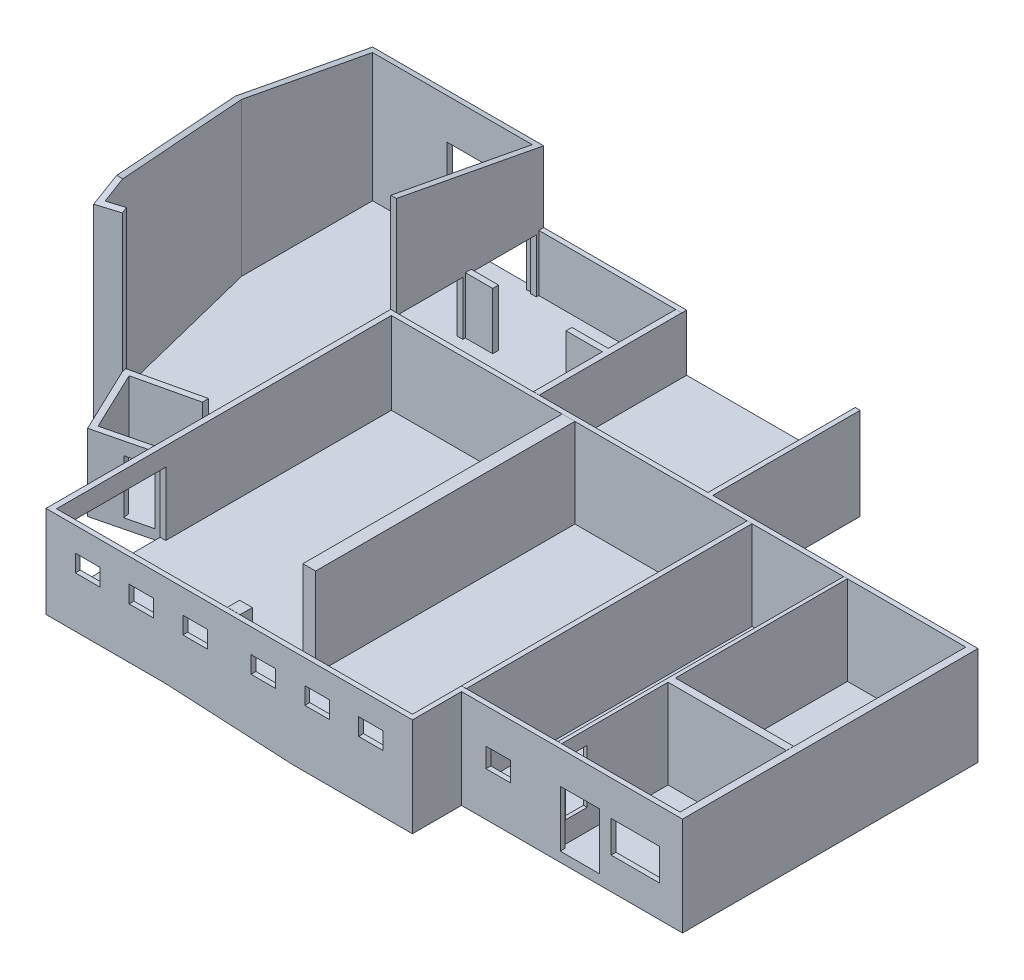
SolidWorks part; units mm, degrees
ref_plane "Ebene vorne" through (0, 0, 0) normal (0, 0, 1) x (1, 0, 0)
ref_plane "Ebene oben" through (0, 0, 0) normal (0, 1, 0) x (1, 0, 0)
ref_plane "Ebene rechts" through (0, 0, 0) normal (1, 0, 0) x (0, 0, -1)
sketch "Skizze1" plane through (0, 0, 0) normal (0, 1, 0) x (1, 0, 0)
  line L0 (14990, -18120) -> (14990, -20130)
  line L1 (0, 0) -> (13180, 0)
  line L4 (24030, -6030) -> (24030, -18120)
  line L5 (13180, 0) -> (13180, -6030)
  line L6 (13180, -6030) -> (24030, -6030)
  line L7 (14990, -20130) -> (0, -20130)
  line L8 (0, -20130) -> (0, 0)
  line L9 (14990, -18120) -> (24030, -18120)
  point P0 (0, 0)
  dimension "D1" = 14990
  dimension "D2" = 20130
  dimension "D3" = 9040
  dimension "D4" = 2010
  dimension "D5" = 13180
  dimension "D6" = 6030
extrude "Aufsatz-Linear austragen4" add sketch "Skizze1" along normal blind 250
sketch "Skizze5" plane through (0, 250, 0) normal (0, 1, 0) x (1, 0, 0)
  line L0 (23730, -6230) -> (23730, -17920)
  line L1 (23730, -17920) -> (14790, -17920)
  line L2 (14790, -17920) -> (14790, -19930)
  line L3 (14790, -19930) -> (230, -19930)
  line L4 (230, -19930) -> (230, -6230)
  line L5 (230, -200) -> (12980, -200)
  line L6 (12980, -200) -> (12980, -6030)
  line L7 (230, -6230) -> (23730, -6230)
  line L8 (24030, -18120) -> (24030, -6030) construction
  line L9 (14990, -18120) -> (24030, -18120) construction
  line L10 (14990, -20130) -> (14990, -18120) construction
  line L11 (0, -20130) -> (14990, -20130) construction
  line L12 (0, 0) -> (0, -20130) construction
  line L13 (13180, 0) -> (0, 0) construction
  line L14 (13180, -6030) -> (13180, 0) construction
  line L15 (24030, -6030) -> (13180, -6030) construction
  line L16 (0, -20130) -> (14990, -20130)
  line L17 (14990, -20130) -> (14990, -18120)
  line L18 (14990, -18120) -> (24030, -18120)
  line L19 (24030, -18120) -> (24030, -6030)
  line L20 (24030, -6030) -> (13180, -6030)
  line L21 (13180, -6030) -> (13180, 0)
  line L22 (13180, 0) -> (0, 0)
  line L23 (0, 0) -> (0, -20130)
  line L24 (12980, -6030) -> (230, -6030)
  line L25 (230, -6030) -> (230, -200)
  dimension "D1" = 300
  dimension "D2" = 200
  dimension "D3" = 200
  dimension "D4" = 200
  dimension "D5" = 230
  dimension "D6" = 200
  dimension "D7" = 200
  dimension "D8" = 200
extrude "Aufsatz-Linear austragen5" add sketch "Skizze5" along normal blind 3635
sketch "Skizze6" plane through (0, 250, 0) normal (0, 1, 0) x (1, 0, 0)
  line L0 (18890, -17920) -> (18890, -13570)
  line L1 (14790, -17920) -> (23730, -17920) construction
  line L2 (23730, -6230) -> (230, -6230) construction
  line L3 (18890, -6230) -> (18740, -6230)
  line L4 (23730, -6230) -> (230, -6230) construction
  line L5 (18740, -6230) -> (18740, -17920)
  line L6 (18740, -17920) -> (18890, -17920)
  line L7 (23730, -17920) -> (23730, -6230) construction
  line L8 (23730, -17920) -> (23730, -6230) construction
  line L9 (18890, -13270) -> (23730, -13270)
  line L11 (18890, -13570) -> (23730, -13570)
  line L12 (23730, -13270) -> (23730, -13570)
  line L13 (18890, -13270) -> (18890, -6230)
  line L14 (14990, -20130) -> (14990, -18120) construction
  line L15 (14790, -17920) -> (14990, -17920)
  line L16 (14790, -17920) -> (14790, -6230)
  line L17 (14790, -6230) -> (14990, -6230)
  line L18 (14990, -17920) -> (14990, -6230)
  line L19 (12980, -200) -> (230, -200) construction
  line L20 (5840, -200) -> (6080, -200)
  line L21 (5840, -200) -> (5840, -2965)
  line L22 (5840, -6030) -> (6080, -6030)
  line L23 (6080, -200) -> (6080, -6030)
  line L24 (230, -6030) -> (12980, -6030) construction
  line L25 (12980, -6030) -> (12980, -200) construction
  line L26 (23730, -6230) -> (230, -6230) construction
  line L27 (7220, -6230) -> (7740, -6230)
  line L28 (7220, -6230) -> (7220, -16840)
  line L29 (7220, -16840) -> (7740, -16840)
  line L30 (7740, -6230) -> (7740, -16840)
  line L31 (230, -19930) -> (14790, -19930) construction
  line L32 (7220, -19430) -> (7740, -19430)
  line L33 (7220, -19430) -> (7220, -19930)
  line L34 (7220, -19930) -> (7740, -19930)
  line L35 (7740, -19430) -> (7740, -19930)
  line L36 (230, -200) -> (230, -6030) construction
  line L37 (230, -2965) -> (1350, -2965)
  line L38 (230, -2965) -> (230, -3205)
  line L39 (230, -3205) -> (1350, -3205)
  line L40 (1350, -2965) -> (1350, -3205)
  line L41 (12980, -200) -> (230, -200) construction
  line L42 (4350, -2965) -> (5840, -2965)
  line L43 (4350, -2965) -> (4350, -3205)
  line L44 (4350, -3205) -> (5840, -3205)
  line L46 (5840, -3205) -> (5840, -6030)
  dimension "D1" = 150
  dimension "D2" = 4840
  dimension "D3" = 4350
  dimension "D4" = 300
  dimension "D5" = 6900
  dimension "D6" = 240
  dimension "D7" = 520
  dimension "D8" = 7050
  dimension "D9" = 500
  dimension "D10" = 2590
  dimension "D11" = 240
  dimension "D12" = 1120
  dimension "D13" = 3000
  dimension "D14" = 2765
extrude "Aufsatz-Linear austragen6" add sketch "Skizze6" along normal blind 3640
sketch "Skizze7" plane through (0, 0, 18120) normal (0, 0, 1) x (1, 0, 0)
  line L0 (24030, 3885) -> (24030, 0) construction
  line L1 (21110, 2450) -> (23090, 2450)
  line L2 (21110, 2450) -> (21110, 1150)
  line L3 (21110, 1150) -> (23090, 1150)
  line L4 (23090, 2450) -> (23090, 1150)
  line L5 (14990, 0) -> (24030, 0) construction
  line L7 (19030, 2550) -> (20630, 2550)
  line L8 (19030, 2550) -> (19030, 250)
  line L9 (19030, 250) -> (20630, 250)
  line L10 (20630, 2550) -> (20630, 250)
  line L11 (15990, 2450) -> (16990, 2450)
  line L12 (15990, 2450) -> (15990, 1650)
  line L13 (15990, 1650) -> (16990, 1650)
  line L14 (16990, 2450) -> (16990, 1650)
  dimension "D1" = 1980
  dimension "D2" = 940
  dimension "D3" = 1150
  dimension "D4" = 2450
  dimension "D5" = 3400
  dimension "D6" = 1600
  dimension "D7" = 250
  dimension "D8" = 2300
  dimension "D9" = 1000
  dimension "D10" = 7040
  dimension "D11" = 800
extrude "Schnitt-Linear austragen1" cut sketch "Skizze7" against normal up to next
sketch "Skizze8" plane through (18890, 0, 0) normal (1, 0, 0) x (0, 0, -1)
  line L0 (-17920, 3885) -> (-17920, 250) construction
  line L1 (-17770, 3310) -> (-16880, 3310)
  line L2 (-17770, 3310) -> (-17770, 1110)
  line L3 (-17770, 1110) -> (-16880, 1110)
  line L4 (-16880, 3310) -> (-16880, 1110)
  line L5 (-17920, 250) -> (-13570, 250) construction
  dimension "D1" = 150
  dimension "D2" = 890
  dimension "D3" = 860
  dimension "D4" = 2200
extrude "Schnitt-Linear austragen2" cut sketch "Skizze8" against normal up to next
sketch "Skizze9" plane through (0, 0, 0) normal (-1, 0, 0) x (0, 0, 1)
  line L0 (0, 0) -> (20130, 0) construction
  line L1 (15460, 3125) -> (19330, 3125)
  line L2 (15460, 3125) -> (15460, 525)
  line L3 (15460, 525) -> (19330, 525)
  line L4 (19330, 3125) -> (19330, 525)
  line L5 (20130, 3885) -> (20130, 0) construction
  line L6 (0, 3885) -> (0, 0) construction
  line L7 (300, 3775) -> (2865, 3775)
  line L8 (300, 3775) -> (300, 1575)
  line L9 (300, 1575) -> (2865, 1575)
  line L10 (2865, 3775) -> (2865, 1575)
  line L11 (3305, 3775) -> (5870, 3775)
  line L12 (3305, 3775) -> (3305, 1575)
  line L13 (3305, 1575) -> (5870, 1575)
  line L14 (5870, 3775) -> (5870, 1575)
  dimension "D1" = 525
  dimension "D2" = 800
  dimension "D3" = 3870
  dimension "D4" = 2600
  dimension "D5" = 1575
  dimension "D6" = 2565
  dimension "D7" = 300
  dimension "D8" = 440
  dimension "D9" = 2200
extrude "Schnitt-Linear austragen3" cut sketch "Skizze9" against normal up to next
sketch "Skizze10" plane through (0, 250, 0) normal (0, 1, 0) x (1, 0, 0)
  line L8 (0, -20130) -> (14990, -20130) construction
  line L9 (0, -14902.5027) -> (0, -15160)
  line L26 (0, -15160) -> (-2621.3867, -15806.7858)
  line L27 (-2621.3867, -15806.7858) -> (-3994.9173, -12922.2993)
  line L28 (0, -12000) -> (-3994.9173, -12922.2993)
  line L29 (0, -14902.5027) -> (-2483.3257, -15515.2241)
  line L30 (-2483.3257, -15515.2241) -> (-3635.3713, -13095.8676)
  line L31 (0, -12256.576) -> (-3635.3713, -13095.8676)
  line L32 (-59.8876, -14917.279) -> (-2483.3257, -15515.2241) construction
  line L34 (56.2378, -12243.5925) -> (-3635.3713, -13095.8676) construction
  line L37 (0, -12000) -> (0, -12256.576)
  dimension "D2" = 2483.3257
  dimension "D3" = 2621.3867
  dimension "D4" = 4970
  dimension "D11" = 4100
  dimension "D12" = 2700
  dimension "D13" = 3160
  dimension "D15" = 250
extrude "Aufsatz-Linear austragen7" add sketch "Skizze10" along normal blind 3000
sketch "Skizze11" plane through (0, 250, 0) normal (0, 1, 0) x (1, 0, 0)
  line L1 (230, -6230) -> (7220, -6230)
  line L2 (230, -6230) -> (230, -19930)
  line L3 (230, -19930) -> (7220, -19930)
  line L4 (7220, -6230) -> (7220, -19930)
extrude "Aufsatz-Linear austragen8" add sketch "Skizze11" along normal blind 275
sketch "Skizze12" plane through (0, 250, 0) normal (0, 1, 0) x (1, 0, 0)
  line L0 (12980, -6030) -> (12980, -200) construction
  line L1 (230, -200) -> (12980, -200)
  line L2 (230, -200) -> (230, -6030)
  line L3 (230, -6030) -> (12980, -6030)
  line L4 (12980, -200) -> (12980, -6030)
extrude "Aufsatz-Linear austragen9" add sketch "Skizze12" along normal blind 1325
sketch "Skizze13" plane through (0, 0, 19930) normal (0, 0, -1) x (-1, 0, 0)
  line L0 (-4895, 525) -> (-10130, 250)
  line L1 (-230, 525) -> (-7220, 525) construction
  line L2 (-7740, 250) -> (-14790, 250) construction
  line L3 (-230, 3885) -> (-230, 525) construction
  line L4 (-4895, 525) -> (-4895, 250)
  line L5 (-4895, 250) -> (-10130, 250)
  dimension "D1" = 4665
  dimension "D2" = 9900
extrude "Aufsatz-Linear austragen10" add sketch "Skizze13" along normal up to surface (3090 mm away) up to face at (7428, 1761, 16840)
sketch "Skizze14" plane through (0, 0, 19930) normal (0, 0, -1) x (-1, 0, 0)
  line L0 (-4895, 525) -> (-10130, 250) construction
  line L1 (-230, 525) -> (-7220, 525) construction
  line L2 (-230, 3885) -> (-230, 525) construction
  line L3 (-4895, 525) -> (-7220, 525)
  line L4 (-7220, 525) -> (-7220, 402.8653)
  line L5 (-7220, 402.8653) -> (-4895, 525)
  dimension "D1" = 4665
extrude "Schnitt-Linear austragen4" cut sketch "Skizze14" along normal up to surface (3090 mm away) up to face at (7428, 1816.6829, 16840)
sketch "Skizze18" plane through (0, 1575, 0) normal (0, 1, 0) x (1, 0, 0)
  line L0 (0, 0) -> (-6770, 0)
  line L1 (-6770, 0) -> (-6770, -5625)
  line L2 (-6770, -5625) -> (-4848.6563, -13331.0887)
  line L3 (-4848.6563, -13331.0887) -> (-3911.5215, -13097.4347)
  line L4 (-3994.9173, -12922.2993) -> (-2621.3867, -15806.7858) construction
  line L5 (0, -240) -> (-6530, -240)
  line L6 (-6530, -240) -> (-6530, -5595.5317)
  line L7 (-6530, -5595.5317) -> (-4673.8466, -13040.1564)
  line L8 (-4673.8466, -13040.1564) -> (-3969.5828, -12864.5637)
  line L9 (0, 0) -> (0, -240)
  line L10 (-3911.5215, -13097.4347) -> (-3969.5828, -12864.5637)
  dimension "D1" = 6770
  dimension "D2" = 5625
  dimension "D3" = 166
  dimension "D4" = 7942
  dimension "D5" = 240
extrude "Aufsatz-Linear austragen12" add sketch "Skizze18" along normal blind 8000
sketch "Skizze19" plane through (0, 1575, 0) normal (0, -1, 0) x (1, 0, 0)
  line L0 (-2621.3867, 15806.7858) -> (0, 15160) construction
  line L1 (-3994.9173, 12922.2993) -> (-2621.3867, 15806.7858) construction
  line L2 (0, 0) -> (0, 20130) construction
  line L3 (0, 0) -> (-6770, 0) construction
  line L4 (-6770, 0) -> (-6770, 5625) construction
  line L5 (-6770, 5625) -> (-4848.6563, 13331.0887) construction
  line L6 (-4848.6563, 13331.0887) -> (-3911.5215, 13097.4347) construction
  line L7 (-2621.3867, 15806.7858) -> (0, 15160)
  line L8 (-3911.5215, 13097.4347) -> (-2621.3867, 15806.7858)
  line L9 (0, 0) -> (0, 15160)
  line L10 (0, 0) -> (-6770, 0)
  line L11 (-6770, 0) -> (-6770, 5625)
  line L12 (-6770, 5625) -> (-4848.6563, 13331.0887)
  line L13 (-4848.6563, 13331.0887) -> (-3911.5215, 13097.4347)
extrude "Aufsatz-Linear austragen13" add sketch "Skizze19" along normal up to surface (1575 mm away) up to face at (13050, 0, 11070)
sketch "Skizze20" plane through (23790, 0, 0) normal (-1, 0, 0) x (0, 0, 1)
  line L0 (6030, 3885) -> (18120, 3885) construction
  line L1 (12075, 3885) -> (12075, 53885) construction
  line L2 (12075, 9126.8586) -> (-1495.4792, 6548.4986) construction
  line L3 (5607.5, 10355) -> (16555, 8276.1322) construction
  line L4 (12075, 9126.8586) -> (21774.9238, 7284.8984) construction
  line L5 (-5340, 8275) -> (5607.5, 10355) construction
  line L6 (12075.0025, 9075.9647) -> (-1187.358, 6556.1464)
  line L7 (12075.0025, 9075.9647) -> (21923.9238, 7205.7107)
  line L8 (12075, 9126.8586) -> (18876.5778, 7835.2778) construction
  line L9 (12075.0025, 9075.9647) -> (18867.2498, 7786.1556) construction
  line L10 (21923.9238, 7205.7107) -> (21923.9238, 13266.9089)
  line L11 (21923.9238, 13266.9089) -> (-1198.8091, 13266.9089)
  line L12 (-1198.8091, 13266.9089) -> (-1187.358, 6556.1464)
  line L13 (12075, 9126.8586) -> (-1196.6909, 6605.2677) construction
  point P6 (12075, 3885)
  dimension "D1" = 50
extrude "Schnitt-Linear austragen8" cut sketch "Skizze20" against normal through all both and the other way through all
sketch "Skizze21" plane through (0, 3885, 0) normal (0, 1, 0) x (1, 0, 0)
  line L0 (230, -3205) -> (230, -6030) construction
  line L1 (0, 0) -> (230, 0)
  line L2 (0, 0) -> (0, -6030)
  line L3 (0, -6030) -> (230, -6030)
  line L4 (230, 0) -> (230, -6030)
  dimension "D1" = 6030
extrude "Aufsatz-Linear austragen14" add sketch "Skizze21" along normal up to surface (2896.7417 mm away)
ref_plane "Ebene1" through (-1200, 0, 0) normal (-1, 0, 0) x (0, 0, 1)
sketch "Skizze22" plane through (-1200, 0, 0) normal (-1, 0, 0) x (0, 0, 1)
  line L0 (9555.4096, 1575) -> (9815.4096, 1575)
  line L1 (5870, 1575) -> (12000, 1575) construction
  line L2 (9815.4096, 1575) -> (9815.4096, 1395)
  line L3 (9815.4096, 1395) -> (10075.4096, 1395)
  line L4 (10075.4096, 1395) -> (10075.4096, 1215)
  line L5 (10075.4096, 1215) -> (10335.4096, 1215)
  line L6 (10335.4096, 1215) -> (10335.4096, 1035)
  line L7 (10335.4096, 1035) -> (10595.4096, 1035)
  line L8 (10595.4096, 1035) -> (10595.4096, 855)
  line L9 (10595.4096, 855) -> (10855.4096, 855)
  line L10 (10855.4096, 855) -> (10855.4096, 675)
  line L12 (10855.4096, 675) -> (13323.1605, 675)
  line L13 (13323.1605, 675) -> (13323.1605, 5461.3971)
  line L14 (13323.1605, 5461.3971) -> (9555.4096, 5461.3971)
  line L15 (9555.4096, 5461.3971) -> (9555.4096, 1575)
  dimension "D1" = 260
  dimension "D2" = 180
extrude "Schnitt-Linear austragen9" cut sketch "Skizze22" against normal up to surface (1200 mm away) up to face at (0, 1825, 17395)
sketch "Skizze23" plane through (0, 1575, 0) normal (0, 1, 0) x (1, 0, 0)
  line L6 (-1200, -13323.1605) -> (-1200, -12533.6179)
  line L7 (-1200, -12533.6179) -> (-3635.3713, -13095.8676)
  line L8 (-3635.3713, -13095.8676) -> (-2483.3257, -15515.2241)
  line L9 (-2483.3257, -15515.2241) -> (0, -14902.5027)
  line L10 (0, -14902.5027) -> (0, -13323.1605)
  line L11 (0, -13323.1605) -> (-1200, -13323.1605)
  line L12 (-1200, -13323.1605) -> (-1200, -12533.6179)
  line L13 (-1200, -12533.6179) -> (-3635.3713, -13095.8676)
  line L14 (-3635.3713, -13095.8676) -> (-2483.3257, -15515.2241)
  line L15 (-2483.3257, -15515.2241) -> (0, -14902.5027)
  line L16 (0, -14902.5027) -> (0, -13323.1605)
  line L17 (0, -13323.1605) -> (-1200, -13323.1605)
  dimension "D1" = 0
extrude "Schnitt-Linear austragen10" cut sketch "Skizze23" against normal up to surface (1050 mm away) up to face at (2515, 525, 15558)
sketch "Skizze24" plane through (3525.8452, 0, 14290.0533) normal (0.2396, 0, 0.9709) x (0.9709, 0, -0.2396)
  line L0 (-3631.5825, 3250) -> (-3631.5825, 0) construction
  line L1 (-5101.5825, 2725) -> (-4061.5825, 2725)
  line L2 (-5101.5825, 2725) -> (-5101.5825, 525)
  line L3 (-5101.5825, 525) -> (-4061.5825, 525)
  line L4 (-4061.5825, 2725) -> (-4061.5825, 525)
  line L5 (-3703.4476, 525) -> (-4630.5072, 525) construction
  dimension "D1" = 1040
  dimension "D2" = 430
  dimension "D3" = 2200
extrude "Schnitt-Linear austragen11" cut sketch "Skizze24" against normal blind 300
sketch "Skizze25" plane through (0, 0, 20130) normal (0, 0, 1) x (1, 0, 0)
  line L0 (0, 0) -> (14990, 0) construction
  line L1 (1200, 2900) -> (2200, 2900)
  line L2 (1200, 2900) -> (1200, 2200)
  line L3 (1200, 2200) -> (2200, 2200)
  line L4 (2200, 2900) -> (2200, 2200)
  line L5 (3400, 2900) -> (4400, 2900)
  line L6 (3400, 2900) -> (3400, 2200)
  line L7 (3400, 2200) -> (4400, 2200)
  line L8 (4400, 2900) -> (4400, 2200)
  line L9 (5600, 2900) -> (6600, 2900)
  line L10 (5600, 2900) -> (5600, 2200)
  line L11 (5600, 2200) -> (6600, 2200)
  line L12 (6600, 2900) -> (6600, 2200)
  line L13 (8390, 2900) -> (9390, 2900)
  line L14 (8390, 2900) -> (8390, 2200)
  line L15 (8390, 2200) -> (9390, 2200)
  line L16 (9390, 2900) -> (9390, 2200)
  line L17 (10590, 2900) -> (11590, 2900)
  line L18 (10590, 2900) -> (10590, 2200)
  line L19 (10590, 2200) -> (11590, 2200)
  line L20 (11590, 2900) -> (11590, 2200)
  line L21 (12790, 2900) -> (13790, 2900)
  line L22 (12790, 2900) -> (12790, 2200)
  line L23 (12790, 2200) -> (13790, 2200)
  line L24 (13790, 2900) -> (13790, 2200)
  line L25 (230, 3885) -> (230, 525) construction
  line L26 (14790, 3885) -> (14790, 250) construction
  dimension "D1" = 1000
  dimension "D2" = 700
  dimension "D3" = 2200
  dimension "D4" = 1200
  dimension "D5" = 970
  dimension "D6" = 1200
  dimension "D7" = 1000
  dimension "D8" = 1200
  dimension "D9" = 1200
extrude "Schnitt-Linear austragen12" cut sketch "Skizze25" against normal up to next
sketch "Skizze26" plane through (0, 0, 200) normal (0, 0, 1) x (1, 0, 0)
  line L0 (12980, 3885) -> (12980, 1575) construction
  line L1 (6080, 1575) -> (12980, 1575)
  line L2 (6080, 1575) -> (6080, 5392.7447)
  line L3 (6080, 5392.7447) -> (12980, 5392.7447)
  line L4 (12980, 1575) -> (12980, 5392.7447)
extrude "Schnitt-Linear austragen13" cut sketch "Skizze26" against normal up to next
sketch "Skizze27" plane through (0, 0, 240) normal (0, 0, 1) x (1, 0, 0)
  line L0 (-6530, 1575) -> (0, 1575) construction
  line L1 (-3490, 5175) -> (-240, 5175)
  line L2 (-3490, 5175) -> (-3490, 1575)
  line L3 (-3490, 1575) -> (-240, 1575)
  line L4 (-240, 5175) -> (-240, 1575)
  line L5 (0, 6827.3412) -> (0, 1575) construction
  dimension "D1" = 3250
  dimension "D2" = 240
  dimension "D3" = 3600
extrude "Schnitt-Linear austragen14" cut sketch "Skizze27" against normal up to next
sketch "Skizze28" plane through (0, 0, 0) normal (0, -1, 0) x (1, 0, 0)
  line L13 (24030, 18120) -> (14990, 18120)
  line L14 (14990, 18120) -> (14990, 20130)
  line L15 (14990, 20130) -> (0, 20130)
  line L16 (0, 20130) -> (0, 15160)
  line L17 (0, 15160) -> (-2621.3867, 15806.7858)
  line L18 (-2621.3867, 15806.7858) -> (-3911.5215, 13097.4347)
  line L19 (-3911.5215, 13097.4347) -> (-4848.6563, 13331.0887)
  line L20 (-4848.6563, 13331.0887) -> (-6770, 5625)
  line L21 (-6770, 5625) -> (-6770, 0)
  line L22 (-6770, 0) -> (13180, 0)
  line L23 (13180, 0) -> (13180, 6030)
  line L24 (13180, 6030) -> (24030, 6030)
  line L25 (24030, 6030) -> (24030, 18120)
  line L26 (24030, 18120) -> (14990, 18120)
  line L27 (14990, 18120) -> (14990, 20130)
  line L28 (14990, 20130) -> (0, 20130)
  line L29 (0, 20130) -> (0, 15160)
  line L30 (0, 15160) -> (-2621.3867, 15806.7858)
  line L31 (-2621.3867, 15806.7858) -> (-3911.5215, 13097.4347)
  line L32 (-3911.5215, 13097.4347) -> (-4848.6563, 13331.0887)
  line L33 (-4848.6563, 13331.0887) -> (-6770, 5625)
  line L34 (-6770, 5625) -> (-6770, 0)
  line L35 (-6770, 0) -> (13180, 0)
  line L36 (13180, 0) -> (13180, 6030)
  line L37 (13180, 6030) -> (24030, 6030)
  line L38 (24030, 6030) -> (24030, 18120)
  dimension "D1" = 0
extrude "Aufsatz-Linear austragen15" add sketch "Skizze28" along normal blind 150
sketch "Skizze29" plane through (0, -150, 0) normal (0, -1, 0) x (1, 0, 0)
  line L0 (13180, 0) -> (13180, 6130)
  line L1 (13180, 6130) -> (7480, 6130)
  line L2 (7480, 6130) -> (7480, 16840)
  line L3 (7220, 16840) -> (7740, 16840) construction
  line L4 (7480, 16840) -> (4895, 16840)
  line L5 (4895, 16840) -> (4895, 20130)
  line L6 (0, 20130) -> (14990, 20130) construction
  line L7 (4895, 20130) -> (0, 20130)
  line L8 (0, 20130) -> (0, 15160)
  line L9 (0, 15160) -> (-2621.3867, 15806.7858)
  line L10 (-2621.3867, 15806.7858) -> (-3911.5215, 13097.4347)
  line L11 (-3911.5215, 13097.4347) -> (-4848.6563, 13331.0887)
  line L12 (-4848.6563, 13331.0887) -> (-6770, 5625)
  line L13 (-6770, 5625) -> (-6770, 0)
  line L14 (-6770, 0) -> (13180, 0)
  line L15 (12980, 6030) -> (12980, 6230) construction
  line L16 (14790, 6230) -> (7740, 6230) construction
  point P31 (12980, 6130)
extrude "Schnitt-Linear austragen15" cut sketch "Skizze29" against normal blind 275
sketch "Skizze30" plane through (0, 125, 0) normal (0, -1, 0) x (1, 0, 0)
  line L0 (-6770, 0) -> (115, 0)
  line L1 (-6770, 0) -> (230, 0) construction
  line L2 (115, 0) -> (115, 9815.4096)
  line L3 (115, 9815.4096) -> (-1400, 9815.4096)
  line L4 (-1400, 9815.4096) -> (-1400, 12451.5035)
  line L6 (-1400, 12451.5035) -> (-3815.1443, 13009.0835)
  line L7 (-3815.1443, 13009.0835) -> (-3911.5215, 13097.4347)
  line L8 (-3911.5215, 13097.4347) -> (-4848.6563, 13331.0887)
  line L9 (-4848.6563, 13331.0887) -> (-6770, 5625)
  line L10 (-6770, 5625) -> (-6770, 0)
  line L11 (0, 6030) -> (230, 6030) construction
  line L12 (0, 6030) -> (0, 240) construction
  line L13 (230, 0) -> (230, 6030) construction
  line L14 (-1200, 12277.0418) -> (-3957.3501, 12913.6263) construction
  line L15 (-3635.3713, 13095.8676) -> (-3861.0875, 13203.3488) construction
  line L16 (-3911.5215, 13097.4347) -> (-2621.3867, 15806.7858) construction
  line L17 (-2483.3257, 15515.2241) -> (-3635.3713, 13095.8676) construction
  line L18 (-3748.2294, 13149.6082) -> (-3815.1443, 13009.0835) construction
  line L19 (-1371.8811, 12573.2997) -> (-1428.1189, 12329.7072) construction
  line L20 (-3635.3713, 13095.8676) -> (-1200, 12533.6179) construction
  line L21 (-1200, 12277.0418) -> (-3957.3501, 12913.6263) construction
  line L23 (-1200, 12277.0418) -> (-1200, 9815.4096) construction
  line L24 (0, 9815.4096) -> (-1200, 9815.4096) construction
  line L25 (0, 5870) -> (0, 9815.4096) construction
  point P24 (115, 6030)
  point P32 (-1400, 12451.5035)
  point P40 (115, 9815.4096)
  point P41 (115, 9645.8833)
  point P46 (230, 5235.9426)
  point P47 (230, 5577.9755)
  point P48 (0, 6030)
  point P51 (230, 6030)
  dimension "D1" = 200
extrude "Schnitt-Linear austragen16" cut sketch "Skizze30" against normal blind 1050
sketch "Skizze31" plane through (0, -150, 0) normal (0, -1, 0) x (1, 0, 0)
  line L0 (4895, 20130) -> (4895, 16840)
  line L1 (4895, 16840) -> (10130, 16840)
  line L2 (10130, 16840) -> (10130, 20130)
  line L3 (0, 20130) -> (14990, 20130) construction
  line L4 (10130, 20130) -> (4895, 20130)
  point P4 (4895, 20303.0379)
extrude "Schnitt-Linear austragen17" cut sketch "Skizze31" against normal offset from surface 400 up to face at (7523.3333, 386.9309, 18788.8889)
sketch "Skizze32" plane through (-1400, 0, 0) normal (-1, 0, 0) x (0, 0, 1)
  line L9 (10455.4096, 275) -> (12451.5035, 275)
  line L11 (12451.5035, 125) -> (12451.5035, 275)
  line L12 (9415.4096, 995) -> (9415.4096, 125)
  line L13 (0, 125) -> (9815.4096, 125) construction
  line L14 (9415.4096, 125) -> (12451.5035, 125)
  line L15 (9815.4096, 125) -> (12451.5035, 125) construction
  line L16 (10455.4096, 455) -> (10455.4096, 275)
  line L17 (10195.4096, 455) -> (10455.4096, 455)
  line L18 (10195.4096, 635) -> (10195.4096, 455)
  line L19 (9935.4096, 635) -> (10195.4096, 635)
  line L20 (9935.4096, 815) -> (9935.4096, 635)
  line L21 (9675.4096, 815) -> (9935.4096, 815)
  line L22 (9675.4096, 995) -> (9675.4096, 815)
  line L23 (9415.4096, 995) -> (9675.4096, 995)
  point P0 (12451.5035, 275)
  dimension "D1" = 1996.0939
  dimension "D2" = 2256.0939
  dimension "D3" = 150
  dimension "D4" = 330
extrude "Schnitt-Linear austragen18" cut sketch "Skizze32" against normal up to surface (1515 mm away) up to face at (115, 650, 4907.7048)
